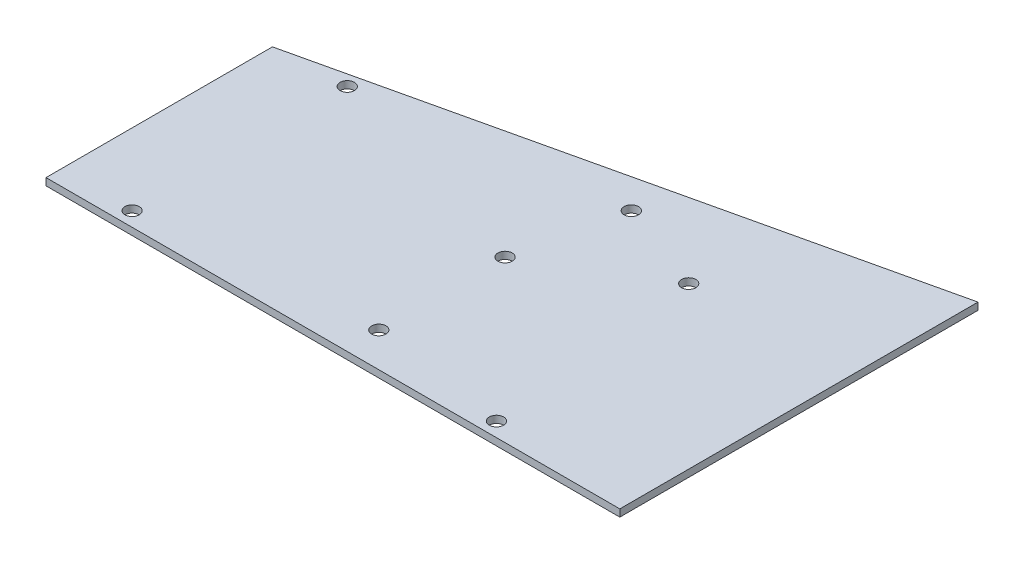
SolidWorks part; units mm, degrees
material "ADK Board"
ref_plane "Front Plane" through (0, 0, 0) normal (0, 0, 1) x (1, 0, 0)
ref_plane "Top Plane" through (0, 0, 0) normal (0, 1, 0) x (1, 0, 0)
ref_plane "Right Plane" through (0, 0, 0) normal (1, 0, 0) x (0, 0, -1)
sketch "Sketch1" plane through (0, 0, 0) normal (0, 1, 0) x (1, 0, 0)
  line L0 (-34.1114, 39.4046) -> (-34.1114, -10.7096)
  line L1 (-34.1114, -10.7096) -> (92.8886, -10.7096)
  line L2 (92.8886, -10.7096) -> (92.8886, 68.5638)
  line L3 (92.8886, 68.5638) -> (-34.1114, 39.4046)
  dimension "D1" = 50.1142
  dimension "D2" = 127
  dimension "D3" = 79.2734
  dimension "D4" = 34.1114
  dimension "D5" = 10.7096
extrude "Boss-Extrude1" add sketch "Sketch1" along normal blind 1.5875
sketch "Sketch2" plane through (0, 1.5875, 0) normal (0, 1, 0) x (1, 0, 0)
  line L0 (-34.1114, 39.4046) -> (-34.1114, -10.7096) construction
  line L1 (-34.1114, -10.7096) -> (92.8886, -10.7096) construction
  line L3 (92.8886, -10.7096) -> (92.8886, 68.5638) construction
  circle A0 centre (-18.2364, 40.0904) radius 1.5875
  circle A1 centre (-18.2364, -7.5346) radius 1.5875
  circle A2 centre (37.0086, 47.7104) radius 1.5875
  circle A3 centre (31.9286, -3.0896) radius 1.5875
  circle A4 centre (31.9286, 24.8504) radius 1.5875
  circle A5 centre (57.3286, 40.0904) radius 1.5875
  circle A6 centre (62.4086, -7.5346) radius 1.5875
  point P20 (-45.1554, 76.0027)
  dimension "D1" = 3.175
  dimension "D4" = 3.175
  dimension "D9" = 3.175
  dimension "D10" = 3.175
  dimension "D14" = 3.175
  dimension "D16" = 3.175
  dimension "D19" = 3.175
  dimension "D2" = 15.875
  dimension "D3" = 50.8
  dimension "D5" = 15.875
  dimension "D6" = 3.175
  dimension "D7" = 58.42
  dimension "D8" = 71.12
  dimension "D11" = 7.62
  dimension "D12" = 66.04
  dimension "D13" = 27.94
  dimension "D15" = 66.04
  dimension "D17" = 50.8
  dimension "D18" = 91.44
  dimension "D20" = 3.175
  dimension "D21" = 30.48
extrude "Cut-Extrude1" cut sketch "Sketch2" against normal through all
